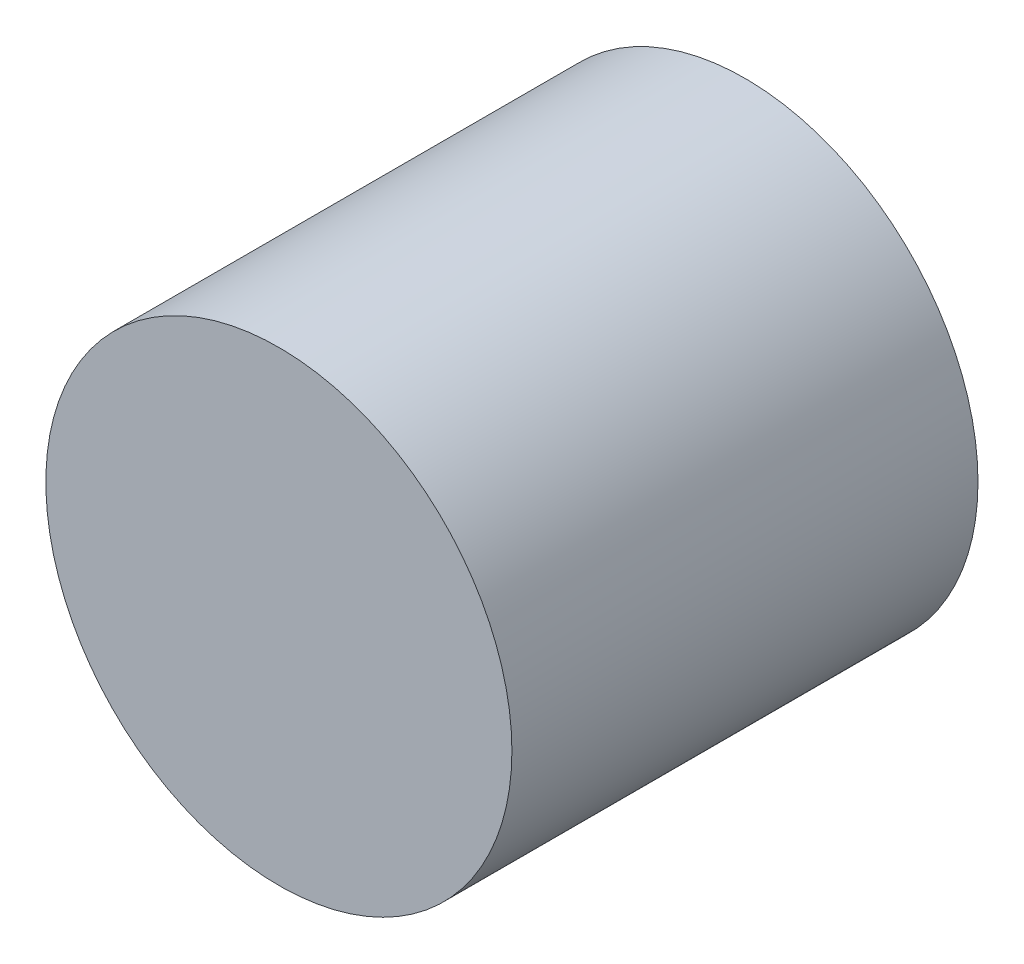
SolidWorks part; units mm, degrees
ref_plane "Alzado" through (0, 0, 0) normal (0, 0, 1) x (1, 0, 0)
ref_plane "Planta" through (0, 0, 0) normal (0, 1, 0) x (1, 0, 0)
ref_plane "Vista lateral" through (0, 0, 0) normal (1, 0, 0) x (0, 0, -1)
sketch "Croquis1" plane through (0, 0, 0) normal (0, 0, 1) x (1, 0, 0)
  circle A0 centre (0, 0) radius 0.25
  dimension "D1" = 0.5
extrude "Saliente-Extruir1" add sketch "Croquis1" along normal blind 0.5
hole_wizard "Diámetro de taladro Ø0.2 (0.2)1" positions "Croquis3" profile "Croquis2" hole size "Ø0.2" standard "ISO"
sketch "Croquis3" plane through (0, 0, 0) normal (0, 0, 1) x (1, 0, 0)
  point P1 (0, 0)
sketch "Croquis2" plane through (0, 0, 0) normal (1, 0, 0) x (0, 1, 0)
  line L0 (0, 0) -> (0, 0.3101)
  line L1 (0, 0.3101) -> (0.1, 0.25)
  line L2 (0.1, 0.25) -> (0.1, 0)
  line L5 (0.1, 0) -> (0, 0)
  line L10 (0, 0.3101) -> (-0.1, 0.25) construction
  line L11 (0, -6.35) -> (0, 107.95) construction
  dimension "Diámetro de taladro" = 0.2
  dimension "Profundidad de taladro" = 0.25
  dimension "Ángulo de perforador" = 118
